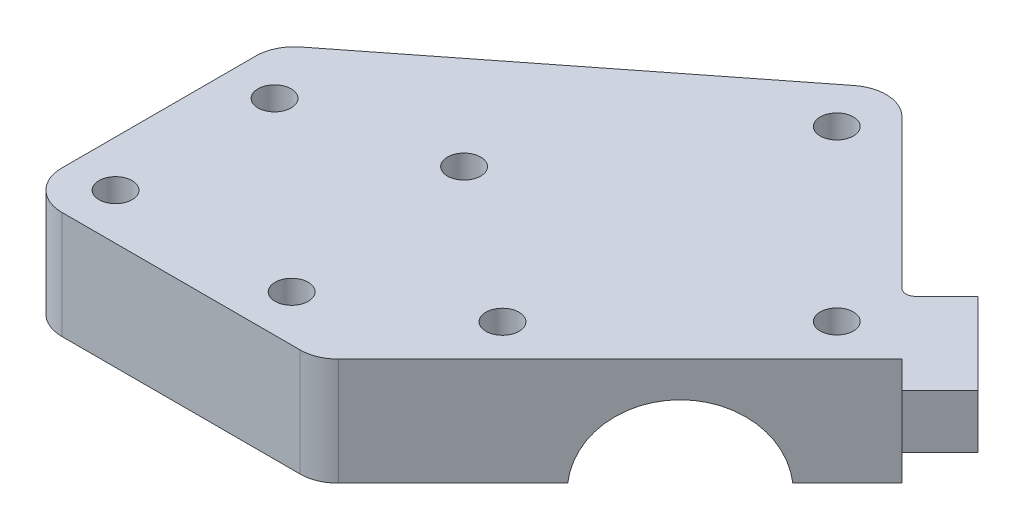
SolidWorks part; units mm, degrees
material "ABS"
ref_plane "前视基准面" through (0, 0, 0) normal (0, 0, 1) x (1, 0, 0)
ref_plane "上视基准面" through (0, 0, 0) normal (0, 1, 0) x (1, 0, 0)
ref_plane "右视基准面" through (0, 0, 0) normal (1, 0, 0) x (0, 0, -1)
ref_plane "基准面4" through (0, 1, 0) normal (0, -1, 0) x (1, 0, 0)
sketch "草图1" plane through (0, 1, 0) normal (0, -1, 0) x (1, 0, 0)
  line L0 (4.7435, -52.275) -> (35.2198, -21.7987)
  line L1 (35.2198, -21.7987) -> (-2.9289, 16.35)
  line L2 (-2.9289, 16.35) -> (-41.0289, 16.35)
  line L3 (-41.0289, 16.35) -> (-41.0289, -16.35)
  line L4 (-41.0289, -16.35) -> (4.7435, -52.275)
extrude "凸台-拉伸1" add sketch "草图1" against normal blind 14
ref_plane "基准面5" through (0, 15, 0) normal (0, 1, 0) x (1, 0, 0)
sketch "草图2" plane through (0, 15, 0) normal (0, 1, 0) x (1, 0, 0)
  line L0 (35.2198, 21.7987) -> (38.7553, 18.2632)
  line L1 (38.7553, 18.2632) -> (43.705, 23.2129)
  line L2 (43.705, 23.2129) -> (33.0984, 33.8195)
  line L3 (33.0984, 33.8195) -> (28.1487, 28.8698)
  line L4 (28.1487, 28.8698) -> (35.2198, 21.7987)
extrude "凸台-拉伸2" add sketch "草图2" against normal blind 7
sketch "草图3" plane through (6.7105, 0, 6.7105) normal (0.7071, 0, 0.7071) x (0.7071, 0, -0.7071)
  line L0 (9.5383, 1) -> (30.27, 1)
  arc A0 (30.27, 1) -> (9.5383, 1) centre (19.9041, 0) ccw
extrude "切除-拉伸1" cut sketch "草图3" against normal blind 38.1
sketch "草图4" plane through (-41.0289, 0, 0) normal (-1, 0, 0) x (0, 0, 1)
  line L0 (-6.2708, 1) -> (6.2708, 1)
  arc A0 (6.2708, 1) -> (-6.2708, 1) centre (0, 0) ccw
extrude "切除-拉伸2" cut sketch "草图4" against normal blind 41.0289
ref_plane "基准面6" through (0, 12, 0) normal (0, 1, 0) x (1, 0, 0)
ref_plane "基准面7" through (0, 17, 0) normal (0, -1, 0) x (1, 0, 0)
hole_wizard "M4 间隙孔1" positions "草图15" profile "草图14" hole size "M4" standard "ANSI Metric"
sketch "草图15" plane through (0, 15, 0) normal (0, 1, 0) x (1, 0, 0)
  point P0 (-35.0289, -10.35)
  point P1 (5, 0)
  point P2 (-15, 15)
  point P3 (-12.103, -10.35)
  point P4 (-35.0289, 10.35)
  point P5 (4.7435, 43.7897)
  point P6 (26.7345, 21.7987)
sketch "草图14" plane through (-35.0289, 15, 10.35) normal (1, 0, 0) x (0, 0, 1)
  line L0 (0, 0) -> (0, 14)
  line L1 (0, 14) -> (2.159, 14)
  line L2 (2.159, 14) -> (2.159, 0)
  line L5 (2.159, 0) -> (0, 0)
  line L11 (0, -6.35) -> (0, 107.95) construction
  dimension "通孔孔直径" = 4.318
  dimension "通孔孔深度" = 14
fillet "圆角1" radius 5 4 edges at (-2.9289, 8, 16.35) (-41.0289, 8, 16.35) (-41.0289, 8, -16.35) (4.7435, 8, -52.275)
fillet "圆角3" radius 1.27 1 edges at (28.1487, 11.5, -28.8698)
fillet "圆角4" radius 1.27 1 edges at (31.2352, 8, -25.7832)
